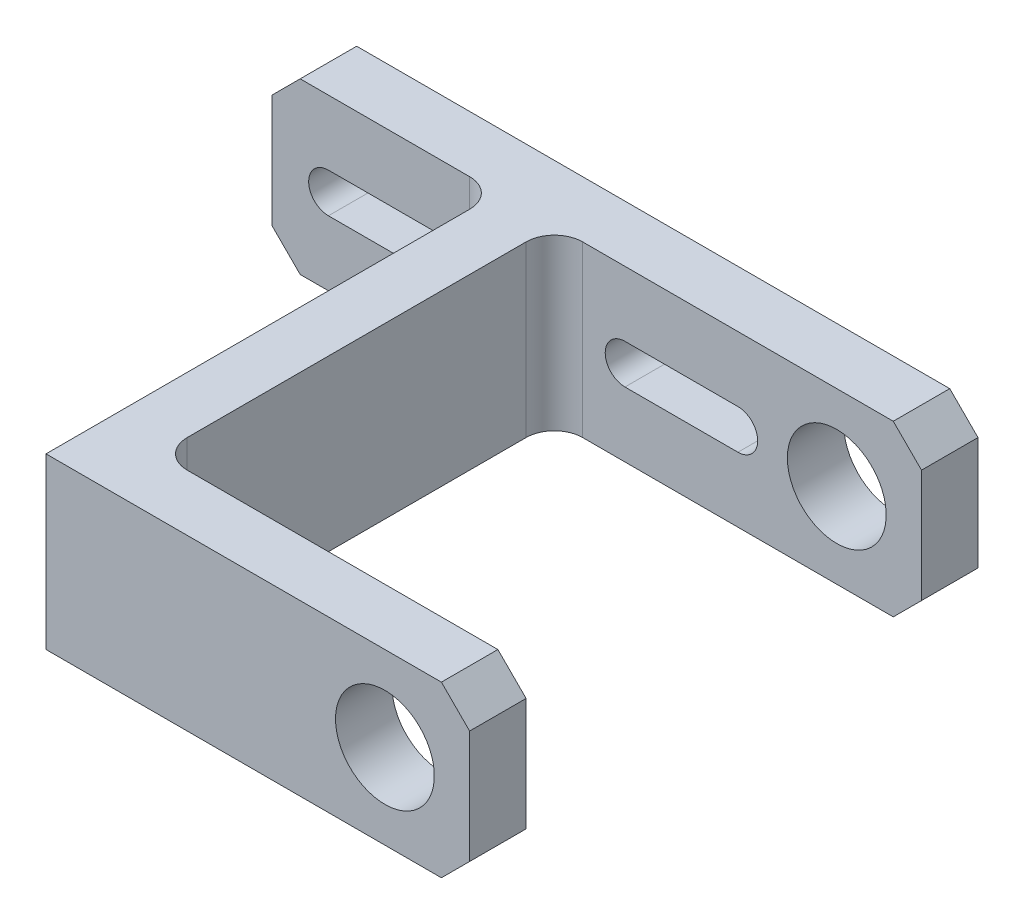
SolidWorks part; units mm, degrees
ref_plane "Front Plane" through (0, 0, 0) normal (0, 0, 1) x (1, 0, 0)
ref_plane "Top Plane" through (0, 0, 0) normal (0, 1, 0) x (1, 0, 0)
ref_plane "Right Plane" through (0, 0, 0) normal (1, 0, 0) x (0, 0, -1)
sketch "Sketch1" plane through (0, 0, 0) normal (0, 1, 0) x (1, 0, 0)
  line L2 (10, 160) -> (10, 10) construction
  line L3 (10, 10) -> (150, 10) construction
  line L4 (0, 160) -> (10, 160)
  line L5 (10, 160) -> (20, 160)
  line L6 (0, 160) -> (0, 0)
  line L7 (0, 0) -> (150, 0)
  line L10 (20, 160) -> (20, 20)
  line L11 (20, 20) -> (150, 20)
  line L17 (150, 0) -> (150, 20)
  line L18 (0, 81.7319) -> (0, 0) construction
  line L19 (10, 81.7319) -> (10, 10) construction
  line L20 (20, 81.7319) -> (20, 20) construction
  point P0 (0, 0)
  dimension "D1" = 10
  dimension "D3" = 150
  dimension "D4" = 160
  dimension "D2" = 10
extrude "Boss-Extrude1" add sketch "Sketch1" along normal mid plane 60
sketch "Sketch3" plane through (0, 0, -160) normal (0, 0, -1) x (-1, 0, 0)
  line L0 (0, 30) -> (0, -30) construction
  line L1 (-150, -30) -> (80, -30)
  line L2 (-150, -30) -> (-150, 30)
  line L3 (-150, 30) -> (80, 30)
  line L4 (80, -30) -> (80, 30)
  line L5 (-150, -30) -> (-20, -30) construction
  line L6 (0, 0) -> (-150, 0) construction
  line L7 (-150, 30) -> (-150, -30) construction
  line L8 (60, 0) -> (20, 0) construction
  line L9 (60, -7) -> (20, -7)
  line L10 (60, 7) -> (20, 7)
  line L11 (-45, 0) -> (-85, 0) construction
  line L12 (-45, -7) -> (-85, -7)
  line L13 (-45, 7) -> (-85, 7)
  arc A0 (60, -7) -> (60, 7) centre (60, 0) ccw
  arc A1 (20, 7) -> (20, -7) centre (20, 0) ccw
  arc A2 (-45, -7) -> (-45, 7) centre (-45, 0) ccw
  arc A3 (-85, 7) -> (-85, -7) centre (-85, 0) ccw
  circle A4 centre (-120, 0) radius 17.5
  point P15 (40, 0)
  point P21 (-65, 0)
  point P29 (58.2957, 0)
  point P30 (0, 0)
  dimension "D3" = 35
  dimension "D8" = 7
  dimension "D1" = 80
  dimension "D2" = 60
  dimension "D4" = 30
  dimension "D5" = 35
  dimension "D6" = 40
  dimension "D7" = 105
extrude "Boss-Extrude2" add sketch "Sketch3" along normal blind 20
fillet "Fillet1" radius 10 3 edges at (0, 0, -160) (20, 0, -160) (20, 0, -20)
chamfer "Chamfer1" distance 10 angle 45 6 edges at (150, -30, -10) (150, 30, -10) (-80, -30, -170) (-80, 30, -170) (150, -30, -170) (150, 30, -170)
sketch "Sketch5" plane through (0, 0, -180) normal (0, 0, -1) x (-1, 0, 0)
  circle A0 centre (-120, 0) radius 17.5 construction
  circle A1 centre (-120, 0) radius 17.5
extrude "Cut-Extrude1" cut sketch "Sketch5" against normal through all both and the other way through all
